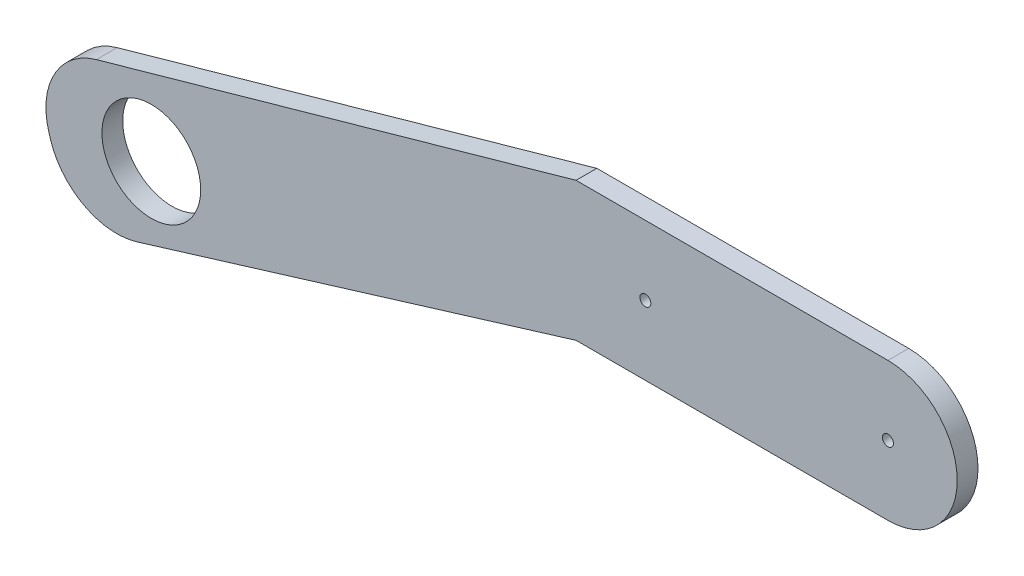
SolidWorks part; units mm, degrees
ref_plane "Alzado" through (0, 0, 0) normal (0, 0, 1) x (1, 0, 0)
ref_plane "Planta" through (0, 0, 0) normal (0, 1, 0) x (1, 0, 0)
ref_plane "Vista lateral" through (0, 0, 0) normal (1, 0, 0) x (0, 0, -1)
sketch "Croquis1" plane through (0, 0, 0) normal (0, 0, 1) x (1, 0, 0)
  line L9 (110.0348, 174.9623) -> (-28.3869, 135.9161)
  line L15 (110.0348, 134.9623) -> (-16.7042, 96.2143)
  line L16 (110.0348, 174.9623) -> (200.0348, 174.9623)
  line L18 (110.0348, 134.9623) -> (200.0348, 134.9623)
  line L20 (-42.0853, 110.8162) -> (-41.6813, 109.4949)
  circle A2 centre (-12.5446, 118.3999) radius 14.25
  circle A12 centre (200.0348, 154.9623) radius 1.58
  circle A13 centre (130.0348, 154.9623) radius 1.58
  arc A18 (-16.7042, 96.2143) -> (-41.6813, 109.4949) centre (-22.5525, 115.3432) cw
  arc A19 (-28.3869, 135.9161) -> (-42.0853, 110.8162) centre (-22.9564, 116.6645) ccw
  arc A20 (200.0348, 174.9623) -> (200.0348, 134.9623) centre (200.0348, 154.9623) cw
  point P9 (-66.0376, 49.2523)
  point P15 (-33.2483, 59.277)
  point P19 (-35.833, 90.3661)
  point P24 (-48.0623, 130.3661)
  dimension "D2" = 40
  dimension "D4" = 28.5
  dimension "D6" = 20
  dimension "D5" = 40
  dimension "D9" = 90
  dimension "D10" = 40
  dimension "D11" = 163
  dimension "D14" = 3.16
  dimension "D8" = 70
  dimension "D3" = 70
  dimension "D7" = 135
extrude "Saliente-Extruir1" add sketch "Croquis1" along normal blind 6
